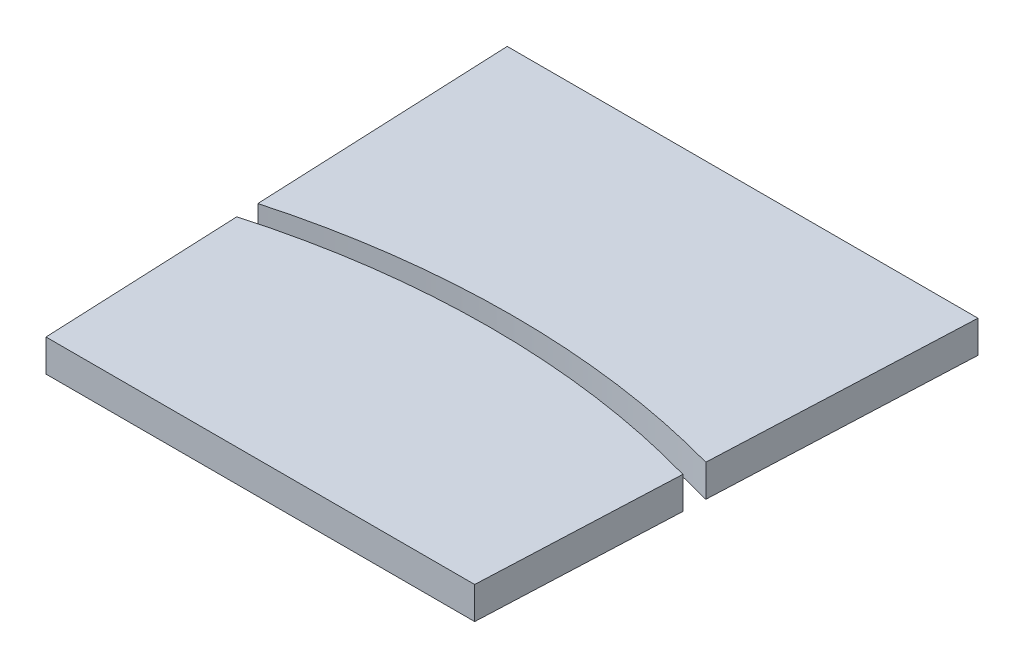
SolidWorks part; units mm, degrees
ref_plane "Front Plane" through (0, 0, 0) normal (0, 0, 1) x (1, 0, 0)
ref_plane "Top Plane" through (0, 0, 0) normal (0, 1, 0) x (1, 0, 0)
ref_plane "Right Plane" through (0, 0, 0) normal (1, 0, 0) x (0, 0, -1)
sketch "Sketch1" plane through (0, 0, 0) normal (0, 1, 0) x (1, 0, 0)
  line L0 (-21.9647, 100) -> (-20, 55)
  line L5 (-21.9647, 100) -> (0, 100)
  line L6 (0, 100) -> (0, 55)
  line L7 (0, 55) -> (-20, 55)
  point P4 (0, 77.5)
  dimension "D1" = 45
  dimension "D2" = 77.5
  dimension "D3" = 2.5
  dimension "D4" = 20
extrude "Boss-Extrude1" add sketch "Sketch1" along normal blind 3
mirror "Mirror2" about plane through (0, 0, 0) normal (1, 0, 0) of "Boss-Extrude1"
sketch "Sketch2" plane through (0, 3, 0) normal (0, 1, 0) x (1, 0, 0)
  line L0 (-21.9647, 100) -> (-20, 55) construction
  line L1 (21.9647, 100) -> (20, 55) construction
  line L2 (-20.8127, 73.6144) -> (-20.9023, 75.666)
  line L3 (20.8127, 73.6144) -> (20.9023, 75.666)
  arc A0 (-20.8127, 73.6144) -> (20.8127, 73.6144) centre (0, 0) cw
  arc A1 (-20.9023, 75.666) -> (20.9023, 75.666) centre (0, 0) cw
  dimension "D1" = 76.5
  dimension "D2" = 78.5
extrude "Cut-Extrude1" cut sketch "Sketch2" against normal through all both and the other way through all
